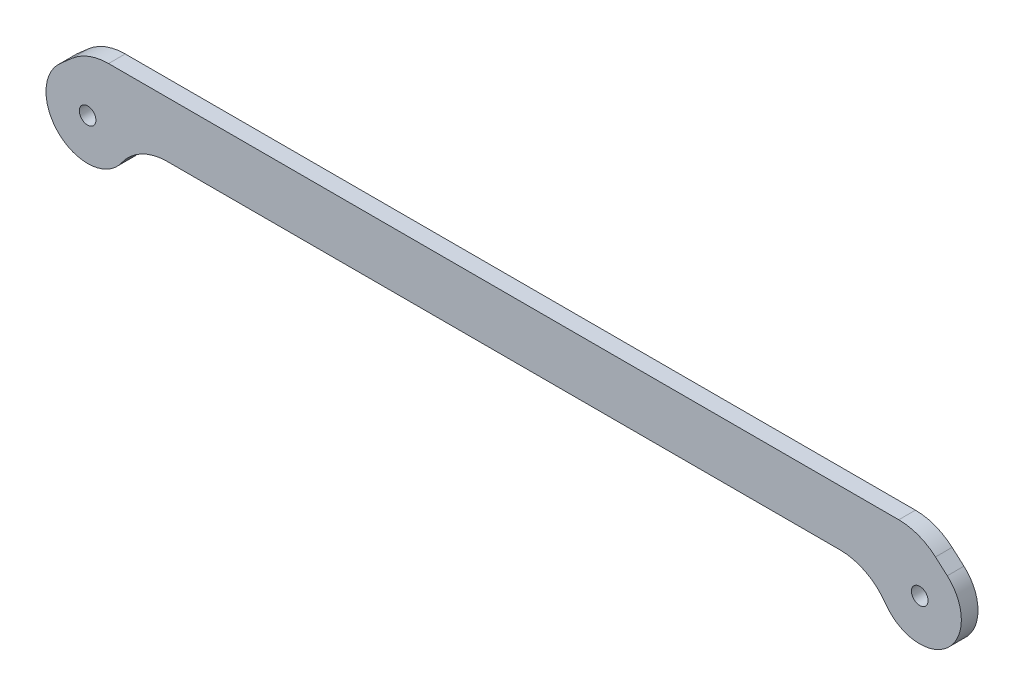
SolidWorks part; units mm, degrees
ref_plane "Front Plane" through (0, 0, 0) normal (0, 0, 1) x (1, 0, 0)
ref_plane "Top Plane" through (0, 0, 0) normal (0, 1, 0) x (1, 0, 0)
ref_plane "Right Plane" through (0, 0, 0) normal (1, 0, 0) x (0, 0, -1)
sketch "Sketch1" plane through (0, 0, 0) normal (0, 0, 1) x (1, 0, 0)
  line L0 (0, 0) -> (150, 0)
  line L1 (0, 10) -> (150, 10)
  line L2 (-4.9608, 5.625) -> (0, 10)
  line L3 (154.9608, 5.625) -> (150, 10)
  circle A0 centre (0, 0) radius 7.5
  circle A1 centre (150, 0) radius 7.5
  circle A2 centre (0, 0) radius 1.5
  circle A3 centre (150, 0) radius 1.5
  dimension "D2" = 15
  dimension "D3" = 15
  dimension "D5" = 3
  dimension "D6" = 3
  dimension "D1" = 150
  dimension "D4" = 10
extrude "Boss-Extrude1" add sketch "Sketch1" along normal blind 3
fillet "Fillet1" radius 10 4 edges at (7.5, 0, 1.5) (142.5, 0, 1.5) (0, 10, 1.5) (150, 10, 1.5)
